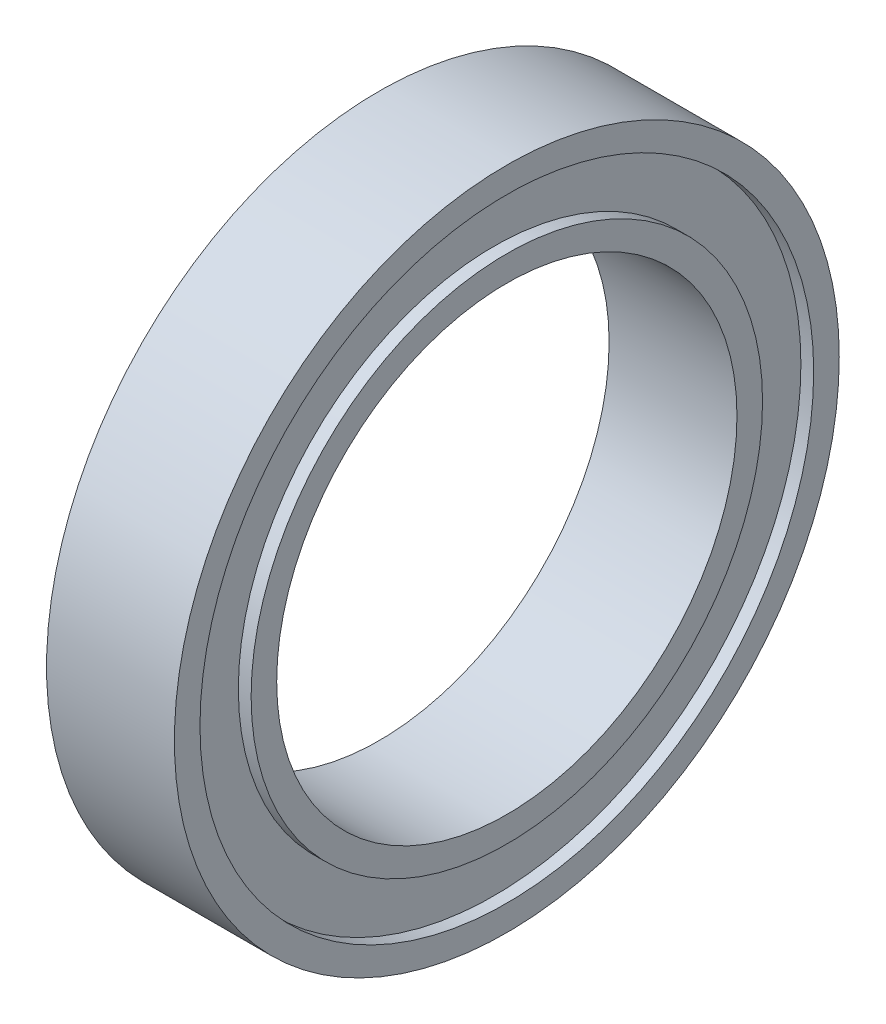
SolidWorks part; units mm, degrees
ref_plane "Front Plane" through (0, 0, 0) normal (0, 0, 1) x (1, 0, 0)
ref_plane "Top Plane" through (0, 0, 0) normal (0, 1, 0) x (1, 0, 0)
ref_plane "Right Plane" through (0, 0, 0) normal (1, 0, 0) x (0, 0, -1)
sketch "Sketch2" plane through (0, 0, 0) normal (1, 0, 0) x (0, 0, -1)
  circle A0 centre (0, 0) radius 13
extrude "Boss-Extrude1" add sketch "Sketch2" along normal mid plane 5
sketch "Sketch3" plane through (2.5, 0, 0) normal (1, 0, 0) x (0, 0, -1)
  circle A0 centre (0, 0) radius 9
extrude "Cut-Extrude1" cut sketch "Sketch3" against normal blind 6
sketch "Sketch4" plane through (2.5, 0, 0) normal (1, 0, 0) x (0, 0, -1)
  circle A0 centre (0, 0) radius 11
  circle A1 centre (0, 0) radius 12
  circle A2 centre (0, 0) radius 10
  dimension "D1" = 1
  dimension "D2" = 1
extrude "Cut-Extrude2" cut sketch "Sketch4" against normal blind 0.5 contours A0 A2 | A1 A0
mirror "Mirror1" about plane through (0, 0, 0) normal (1, 0, 0) of "Cut-Extrude2"
